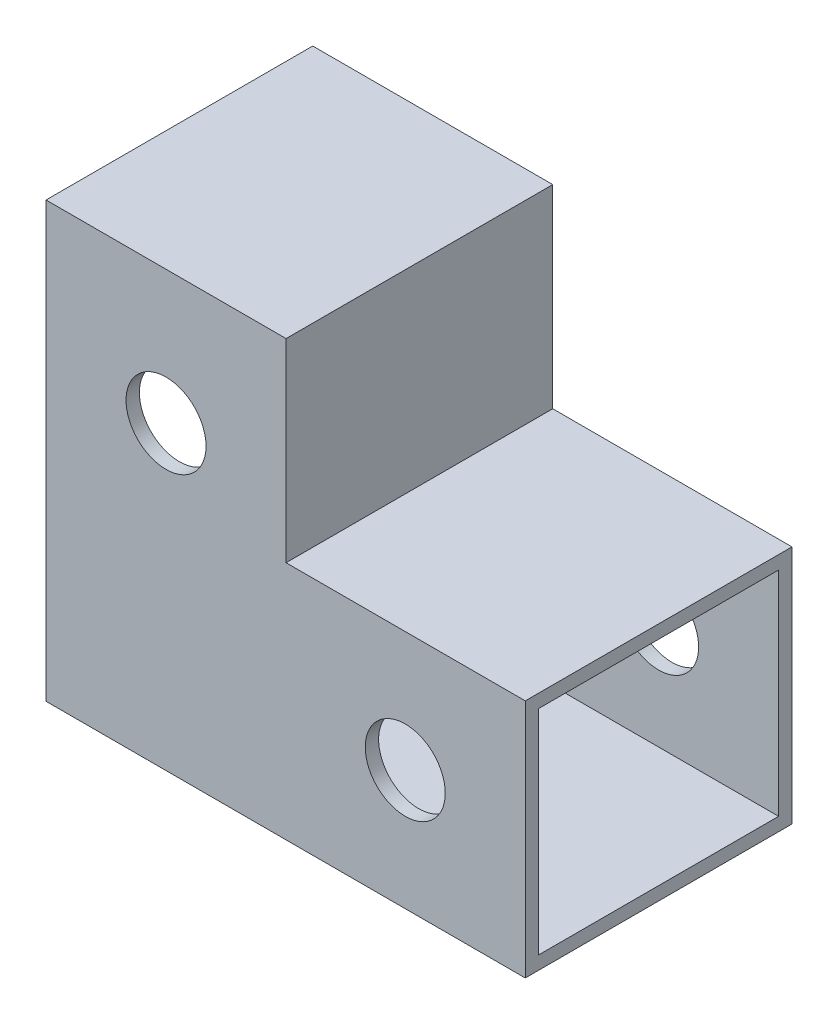
SolidWorks part; units mm, degrees
ref_plane "Front Plane" through (0, 0, 0) normal (0, 0, 1) x (1, 0, 0)
ref_plane "Top Plane" through (0, 0, 0) normal (0, 1, 0) x (1, 0, 0)
ref_plane "Right Plane" through (0, 0, 0) normal (1, 0, 0) x (0, 0, -1)
sketch "Sketch4" plane through (0, 0, 0) normal (0, 0, 1) x (1, 0, 0)
  line L0 (0, 0) -> (0, 13.56) construction
  line L1 (0, 13.56) -> (-17.94, 13.56) construction
  line L2 (-26.94, 23.56) -> (-26.94, -9)
  line L3 (-26.94, -9) -> (9, -9)
  line L4 (9, -9) -> (9, 9)
  line L5 (9, 9) -> (-8.94, 9)
  line L6 (-8.94, 9) -> (-8.94, 23.56)
  line L7 (-8.94, 23.56) -> (-26.94, 23.56)
  circle A0 centre (-17.94, 13.56) radius 3
  circle A1 centre (0, 0) radius 3
  dimension "D3" = 6
  dimension "D1" = 17.94
  dimension "D2" = 13.56
  dimension "D4" = 9
  dimension "D5" = 18
  dimension "D6" = 9
  dimension "D7" = 9
  dimension "D8" = 9
  dimension "D9" = 10
extrude "Boss-Extrude1" add sketch "Sketch4" along normal blind 20 contours L6 L7 L2 L3 L4 L5 A1 A0
sketch "Sketch5" plane through (9, 0, 0) normal (1, 0, 0) x (0, 0, -1)
  line L0 (-1, 8) -> (-19, 8)
  line L1 (-19, 8) -> (-19, -8)
  line L2 (-19, -8) -> (-1, -8)
  line L3 (-1, -8) -> (-1, 8)
  line L4 (0, -9) -> (0, 9)
  line L5 (0, 9) -> (-20, 9)
  line L6 (-20, 9) -> (-20, -9)
  line L7 (-20, -9) -> (0, -9)
  line L8 (0, -9) -> (0, 9)
  line L9 (0, 9) -> (-20, 9)
  line L10 (-20, 9) -> (-20, -9)
  line L11 (-20, -9) -> (0, -9)
  dimension "D1" = 0
  dimension "D2" = 1
extrude "Cut-Extrude3" cut sketch "Sketch5" against normal through all contours L2 L3 L0 L1
sketch "Sketch6" plane through (-26.94, 0, 0) normal (-1, 0, 0) x (0, 0, 1)
  line L0 (1, 22.56) -> (1, -8)
  line L1 (1, -8) -> (19, -8)
  line L2 (19, -8) -> (19, 22.56)
  line L3 (19, 22.56) -> (1, 22.56)
  line L4 (0, 23.56) -> (0, -9)
  line L5 (0, -9) -> (20, -9)
  line L6 (20, -9) -> (20, 23.56)
  line L7 (20, 23.56) -> (0, 23.56)
  line L8 (0, 23.56) -> (0, -9)
  line L9 (0, -9) -> (20, -9)
  line L10 (20, -9) -> (20, 23.56)
  line L11 (20, 23.56) -> (0, 23.56)
  line M12 (1, 8) -> (19, 8)
  dimension "D1" = 0
  dimension "D2" = 1
extrude "Cut-Extrude4" cut sketch "Sketch6" against normal blind 17 contours L2 L3 L0 M12
